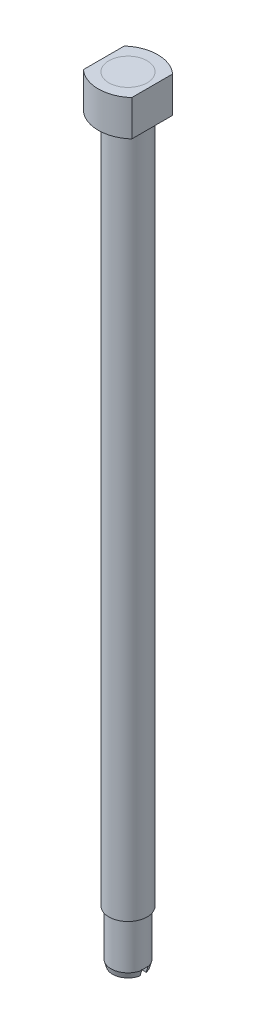
SolidWorks part; units mm, degrees
ref_plane "Front Plane" through (0, 0, 0) normal (0, 0, 1) x (1, 0, 0)
ref_plane "Top Plane" through (0, 0, 0) normal (0, 1, 0) x (1, 0, 0)
ref_plane "Right Plane" through (0, 0, 0) normal (1, 0, 0) x (0, 0, -1)
sketch "Sketch1" plane through (0, 0, 0) normal (0, 1, 0) x (1, 0, 0)
  circle A0 centre (0, 0) radius 3.175
  dimension "D1" = 6.35
extrude "Boss-Extrude1" add sketch "Sketch1" along normal blind 119.761
sketch "Sketch2" plane through (0, 0, 0) normal (0, -1, 0) x (1, 0, 0)
  circle A0 centre (0, 0) radius 2.8229
  dimension "D1" = 5.6457
extrude "Boss-Extrude5" add sketch "Sketch2" along normal blind 7.62
sketch "Sketch10" plane through (0, 0, 0) normal (1, 0, 0) x (0, 0, -1)
  line L0 (0, 0) -> (0, -7.62) construction
  line L1 (-2.8229, -7.62) -> (2.8229, -7.62) construction
  line L2 (0, -7.62) -> (2.8229, -7.62) construction
  line L3 (2.8229, -7.62) -> (2.5605, -8.5425)
  line L4 (2.5605, -8.5425) -> (0, -8.5425)
  line L5 (0, -8.5425) -> (0, -7.62)
  line L6 (0, -7.62) -> (2.8229, -7.62)
  dimension "D1" = 0.9225
  dimension "D2" = 2.5605
revolve "Revolve1" add sketch "Sketch10" angle 360 about L0
sketch "Sketch11" plane through (0, -8.5425, 0) normal (0, -1, 0) x (1, 0, 0)
  line L0 (0, 0.508) -> (0, -0.508)
  line L1 (-2.5096, 0.508) -> (2.5096, 0.508)
  line L2 (2.5096, 0.508) -> (2.8543, 0.508)
  line L3 (2.8543, 0.508) -> (2.8543, -0.508)
  line L4 (2.8543, -0.508) -> (-2.8543, -0.508)
  line L5 (-2.8543, 0.508) -> (-2.8543, -0.508)
  line L6 (-2.5096, 0.508) -> (-2.8543, 0.508)
  circle A0 centre (0, 0) radius 2.5605 construction
  point P4 (0, 0)
  circle M6 centre (0, 0) radius 2.5605
  dimension "D1" = 1.016
  dimension "D2" = 0.3447
extrude "Cut-Extrude1" cut sketch "Sketch11" against normal blind 1.016 contours L4 L0 L1 M6 | L4 L1 L0 M6 | L6 L5 L4 M6 | L4 L3 L2 M6
sketch "Sketch12" plane through (0, 119.761, 0) normal (0, 1, 0) x (1, 0, 0)
  line L0 (0, 0) -> (0, 4.9276) construction
  line L1 (0, 0) -> (0, -4.9276) construction
  line L2 (0, 0) -> (-4.0132, 0) construction
  line L3 (0, 0) -> (4.0132, 0) construction
  line L4 (-4.0132, -3.3909) -> (-4.0132, 3.3909)
  line L5 (4.0132, -3.3909) -> (4.0132, 3.3909)
  circle A0 centre (0, 0) radius 3.175
  arc A1 (4.0132, -3.3909) -> (-4.0132, -3.3909) centre (0, 1.0811) cw
  arc A2 (-4.0132, 3.3909) -> (4.0132, 3.3909) centre (0, -1.0811) cw
  point P10 (-4.0132, 0)
  point P13 (4.0132, 0)
  point P14 (0, -4.9276)
  point P16 (0, 4.9276)
  dimension "D1" = 6.35
  dimension "D2" = 9.8552
  dimension "D3" = 8.0264
  dimension "D4" = 6.7818
extrude "Boss-Extrude6" add sketch "Sketch12" against normal blind 5.9436 separate body
